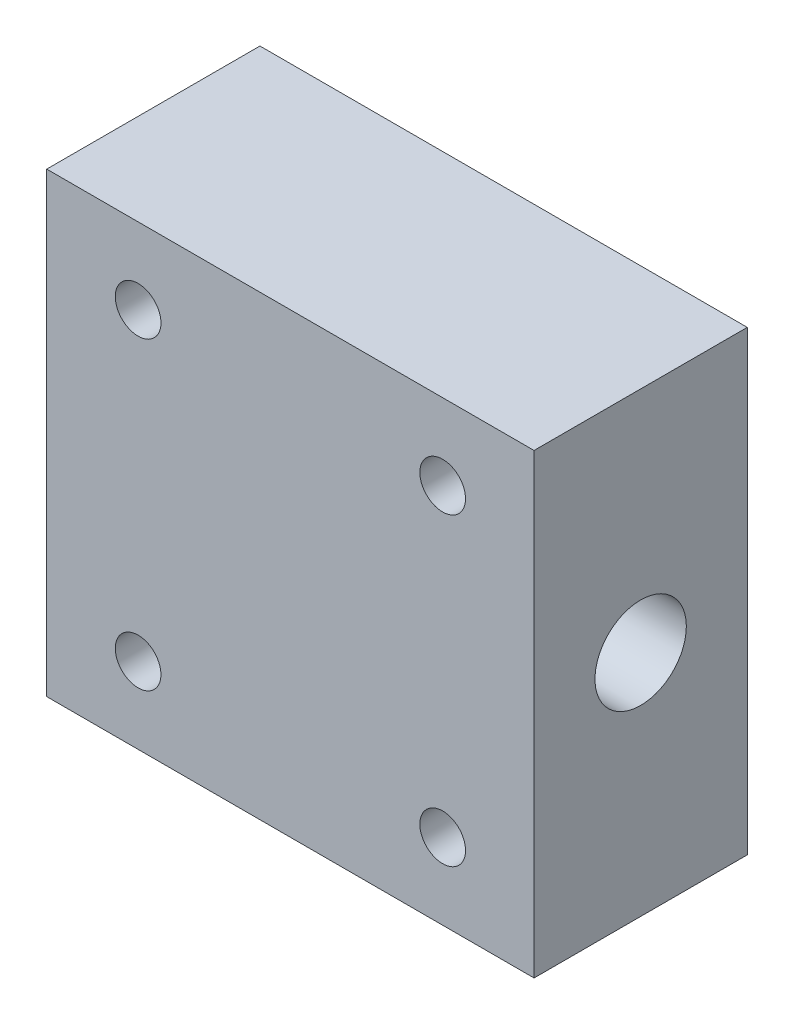
SolidWorks part; units mm, degrees
material "铸造不锈钢"
ref_plane "前视基准面" through (0, 0, 0) normal (0, 0, 1) x (1, 0, 0)
ref_plane "上视基准面" through (0, 0, 0) normal (0, 1, 0) x (1, 0, 0)
ref_plane "右视基准面" through (0, 0, 0) normal (1, 0, 0) x (0, 0, -1)
other "Configuration Table"
sketch "草图1" plane through (0, 0, 0) normal (0, 0, 1) x (1, 0, 0)
  line L1 (-16, -15) -> (16, -15)
  line L2 (-16, -15) -> (-16, 15)
  line L3 (-16, 15) -> (16, 15)
  line L4 (16, -15) -> (16, 15)
  line L5 (-16, -15) -> (16, 15) construction
  line L6 (-16, 15) -> (16, -15) construction
  point P0 (0, 0)
  dimension "D1" = 32
  dimension "D2" = 30
extrude "凸台-拉伸1" add sketch "草图1" along normal blind 14
sketch "草图2" plane through (16, 0, 0) normal (1, 0, 0) x (0, 0, -1)
  line L0 (0, -15) -> (0, 15) construction
  line L1 (-14, -15) -> (0, -15) construction
  circle A0 centre (-7, 0) radius 3
  dimension "D1" = 6
  dimension "D2" = 7
  dimension "D3" = 15
extrude "切除-拉伸1" cut sketch "草图2" against normal blind 33
sketch "草图3" plane through (0, 0, 14) normal (0, 0, 1) x (1, 0, 0)
  line L0 (-1000, 0) -> (49000, 0) construction
  line L1 (0, -1000) -> (0, 49000) construction
  line L2 (16, 15) -> (-16, 15) construction
  circle A0 centre (-10, 10) radius 1.5
  circle A1 centre (10, 10) radius 1.5
  circle A2 centre (10, -10) radius 1.5
  circle A3 centre (-10, -10) radius 1.5
  dimension "D1" = 3
  dimension "D2" = 5
  dimension "D3" = 10
extrude "切除-拉伸2" cut sketch "草图3" against normal blind 3
